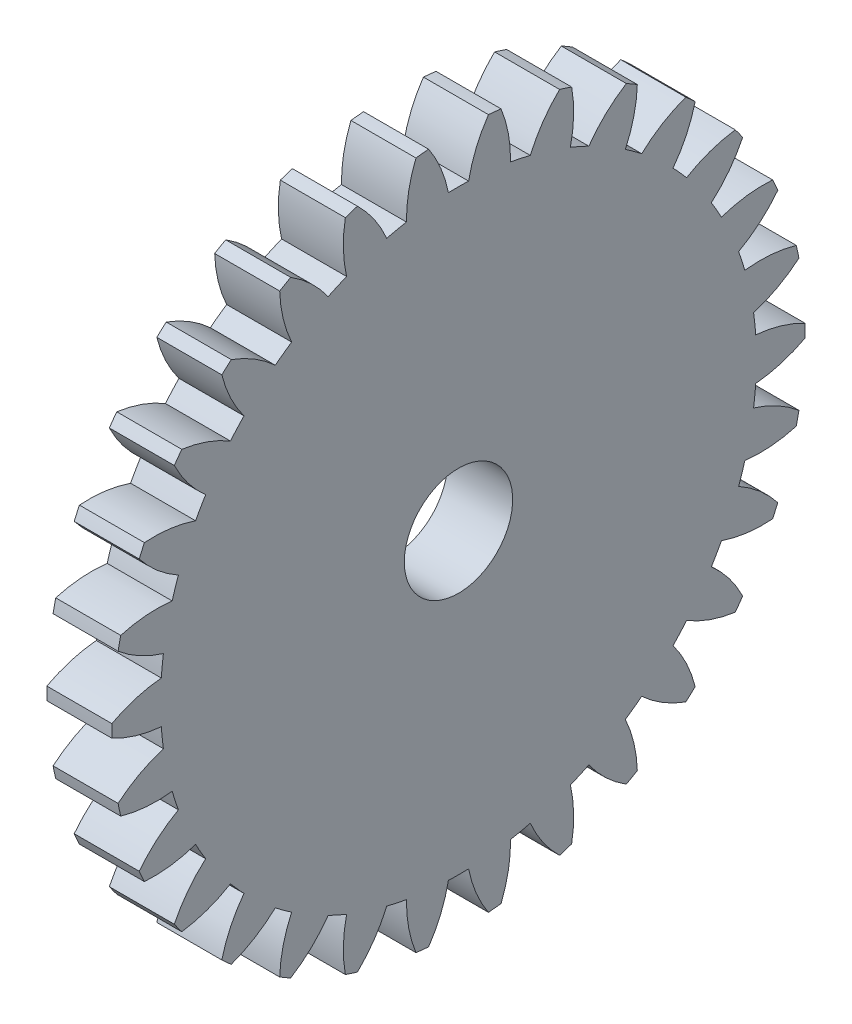
SolidWorks part; units mm, degrees
ref_plane "Plane1" through (0, 0, 0) normal (0, 0, 1) x (1, 0, 0)
ref_plane "Plane2" through (0, 0, 0) normal (0, 1, 0) x (1, 0, 0)
ref_plane "Plane3" through (0, 0, 0) normal (1, 0, 0) x (0, 0, -1)
sketch "HoldingSke" plane through (0, 0, 0) normal (0, 1, 0) x (1, 0, 0)
  line L0 (0, 0) -> (0.866, -0.5)
  line L1 (-15, 0) -> (100, 0) construction
  line L2 (0, 0) -> (-2.1039, 2.3779)
  line L3 (0, 0) -> (-11.863, 4.5341)
  line L4 (0, 0) -> (7.479, 4.318)
  line L5 (0, 0) -> (-46.8476, -17.4728)
  line L6 (0, 0) -> (-2.4869, -1.6779)
  line L7 (-2.1039, 2.3779) -> (8.6586, 51.2059)
  line L8 (-76.2, 54.61) -> (-75.3, 54.61)
  line L9 (-71.009, 38.7566) -> (-53.1078, 45.2721)
  line L10 (-76.2, 71.12) -> (104.1128, 71.12)
  line L11 (0, 0) -> (-3, 0)
  line L12 (-76.2, 101.6) -> (-76.162, 101.6)
  line L13 (24.9733, 27.94) -> (52.9518, 28.4284)
  line L14 (24.9733, 27.94) -> (24.9743, 27.94)
  line L15 (24.9733, 27.94) -> (100.4006, 29.5858)
  line L16 (-63.627, -1) -> (-12.827, -1)
  circle A0 centre (0, 0) radius 2.5
  circle A1 centre (0, 0) radius 13.749
  circle A2 centre (0, 0) radius 37.5
  circle A3 centre (0, 0) radius 2.5
  dimension "MHD" = 27.498
  dimension "Hub_dia" = 75
  dimension "Bore" = 5
  dimension "MBD" = 5
  dimension "Num_teeth" = 30
  dimension "Pitch_radius" = 180.3128
  dimension "Pitch" = 1
  dimension "Width" = 3
  dimension "Overall_len" = 50
  dimension "Show_teeth" = 30
  dimension "Thickness" = 3
  dimension "OAL" = 50.0001
  dimension "T_dim" = 0.9
  dimension "Ap" = 20
  dimension "H" = 19.05
  dimension "Backlash" = 0.038
  dimension "Addendum_fac" = 1
  dimension "Dedendum_fac" = 1.25
  dimension "Clearance_fac" = 0.25
  dimension "Dedendum_add" = 0.001
  dimension "Module" = 1
sketch "BasProSke" plane through (0, 0, 0) normal (0, 1, 0) x (1, 0, 0)
  line L0 (-10, 0) -> (60, 0) construction
  line L1 (0, 0) -> (0, 16)
  line L2 (0, 0) -> (3, 0)
  line L3 (3, 0) -> (3, 16)
  line L4 (3, 16) -> (0, 16)
  dimension "Diameter" = 32
  dimension "Thickness" = 3
revolve "Base-Revolve" add sketch "BasProSke" angle 360 about L0
sketch "TooCutSke" plane through (0, 0, 0) normal (1, 0, 0) x (0, 0, -1)
  line L1 (0, 0) -> (0, 107) construction
  line L2 (0, 0) -> (-0.8515, 14.9758) construction
  line L3 (0, 0) -> (-3.1323, 29.8014) construction
  line L4 (-0.8515, 14.9758) -> (-1.5661, 14.9007) construction
  arc A0 (0.4664, 13.7411) -> (-0.4664, 13.7411) centre (0, 0) ccw
  arc A1 (1.3975, 15.9644) -> (-1.3975, 15.9644) centre (0, 0) ccw
  circle A2 centre (0, 0) radius 15 construction
  circle A3 centre (0, 0) radius 14.0954 construction
  arc A4 (-0.4664, 13.7411) -> (-1.3975, 15.9644) centre (-6.3534, 12.5823) ccw
  arc A5 (1.3975, 15.9644) -> (0.4664, 13.7411) centre (6.3534, 12.5823) ccw
  dimension "Root_dia" = 27.498
  dimension "Overcut_dia" = 32.0508
  dimension "Pitch_dia" = 30
  dimension "Base_dia" = 28.1908
  dimension "Flank_rad" = 6
  dimension "Half_ang" = 6
  dimension "Half_CT" = 0.7185
extrude "ToothCut" cut sketch "TooCutSke" along normal through all
fillet "Breaks" [suppressed] radius 0.02
fillet "RootFillets" [suppressed] radius 0.251
pattern_circular "TeethCuts" count 30 every 12 about axis through (-10, 0, 0) along (1, 0, 0) of "ToothCut", "RootFillets", "Breaks"
sketch "HubNeaOneSke" plane through (0, 0, 0) normal (-1, 0, 0) x (0, 0, 1)
  circle A0 centre (0, 0) radius 13.749
  dimension "Diameter" = 27.498
extrude "HubNearOne" [suppressed] add sketch "HubNeaOneSke" along normal blind 47.0001
sketch "HubNeaBotSke" plane through (0, 0, 0) normal (-1, 0, 0) x (0, 0, 1)
  circle A0 centre (0, 0) radius 13.749
  dimension "Diameter" = 27.498
extrude "HubNearBoth" [suppressed] add sketch "HubNeaBotSke" along normal blind 23.5
ref_plane "FarPln" through (3, 0, 0) normal (1, 0, 0) x (0, 0, -1)
sketch "HubFarSke" plane through (3, 0, 0) normal (1, 0, 0) x (0, 0, -1)
  circle A0 centre (0, 0) radius 13.749
  dimension "Diameter" = 27.498
extrude "HubFar" [suppressed] add sketch "HubFarSke" along normal blind 23.5
sketch "BorSke" plane through (0, 0, 0) normal (1, 0, 0) x (0, 0, -1)
  circle A0 centre (0, 0) radius 2.5
  dimension "Diameter" = 5
extrude "Bore" cut sketch "BorSke" along normal mid plane 100.0001
sketch "KeySke" plane through (0, 0, 0) normal (1, 0, 0) x (0, 0, -1)
  line L0 (-1, 0) -> (-1, 3.4)
  line L1 (-1, 3.4) -> (1, 3.4)
  line L2 (1, 3.4) -> (1, 0)
  line L3 (0, 0) -> (0, 34) construction
  line L4 (-1, 0) -> (1, 0)
  dimension "Offset" = 3.4
  dimension "Width" = 2
extrude "Keyway" [suppressed] cut sketch "KeySke" along normal mid plane 100.0001
pattern_circular "Keyway2" [suppressed] count 2 every 90 about axis through (-10, 0, 0) along (1, 0, 0)
equation "' \"Module@HoldingSke\" = 6.35"
equation "' \"Num_teeth@HoldingSke\" = 12"
equation "' \"Ap@HoldingSke\" =  20"
equation "' \"Width@HoldingSke\" = 0.5 * 25.4"
equation "' \"Hub_dia@HoldingSke\"= 1 * 25.4"
equation "' \"Overall_len@HoldingSke\" = 1.0 * 25.4"
equation "' \"Bore@HoldingSke\" = 0.75 * 25.4"
equation "' \"T_dim@HoldingSke\" = 0.1 * 25.4"
equation "' \"Width@KeySke\" = 0.25 * 25.4"
equation "' \"Show_teeth@HoldingSke\" = 13"
equation "' \"Backlash@HoldingSke\" = 0.009 * 25.4"
equation "' \"Addendum_fac@HoldingSke\" = 1.0"
equation "' \"Dedendum_fac@HoldingSke\" = 1.25"
equation "' \"Dedendum_add@HoldingSke\" = 0.00005 * 25.4"
equation "' \"Clearance_fac@HoldingSke\" = 0.25"
equation "\"Pitch@HoldingSke\" = 1 / \"Module@HoldingSke\""
equation "\"Overcut_dia@TooCutSke\" = (\"Num_teeth@HoldingSke\" + 2 * \"Addendum_fac@HoldingSke\") / \"Pitch@HoldingSke\" + 0.002 * 25.4"
equation "\"Pitch_dia@TooCutSke\" = \"Num_teeth@HoldingSke\" / \"Pitch@HoldingSke\""
equation "\"Base_dia@TooCutSke\" = \"Num_teeth@HoldingSke\" / \"Pitch@HoldingSke\" * cos((\"Ap@HoldingSke\"  * 3.14159265 / 180))"
equation "\"Root_dia@TooCutSke\" = (\"Num_teeth@HoldingSke\" + 2) / \"Pitch@HoldingSke\" - 2 * (\"Addendum_fac@HoldingSke\" + \"Dedendum_fac@HoldingSke\") / \"Pitch@HoldingSke\" - \"Dedendum_add@HoldingSke\" * 2"
equation "\"Half_ang@TooCutSke\" = 180 / \"Num_teeth@HoldingSke\""
equation "\"Half_CT@TooCutSke\" = \"Num_teeth@HoldingSke\" / \"Pitch@HoldingSke\" * sin((3.14159265 / 2 / \"Num_teeth@HoldingSke\")) / 2 - 7 * \"Backlash@HoldingSke\" / 4"
equation "\"Flank_rad@TooCutSke\" = \"Num_teeth@HoldingSke\" / \"Pitch@HoldingSke\" / 5"
equation "\"Radius@RootFillets\" = \"Clearance_fac@HoldingSke\" / \"Pitch@HoldingSke\" + \"Dedendum_add@HoldingSke\""
equation "\"Break_rad@Breaks\" = 0.02 / \"Pitch@HoldingSke\""
equation "\"Thickness@HoldingSke\" = \"Width@HoldingSke\""
equation "\"OAL@HoldingSke\" = \"Thickness@HoldingSke\""
equation "\"MHD@HoldingSke\" = (\"Num_teeth@HoldingSke\" + 2) / \"Pitch@HoldingSke\" - 2 * (\"Addendum_fac@HoldingSke\" + \"Dedendum_fac@HoldingSke\")  / \"Pitch@HoldingSke\" - \"Dedendum_add@HoldingSke\" * 2"
equation "\"MBD@HoldingSke\" = (\"Num_teeth@HoldingSke\" + 2) / \"Pitch@HoldingSke\" - 2 * (\"Addendum_fac@HoldingSke\" + \"Dedendum_fac@HoldingSke\")  / \"Pitch@HoldingSke\" - \"Dedendum_add@HoldingSke\" * 2 - 0.002 * 25.4"
equation "\"MHD@HoldingSke\" = ((sgn( \"MHD@HoldingSke\" - \"Hub_dia@HoldingSke\" )-1)*( \"MHD@HoldingSke\" - \"Hub_dia@HoldingSke\" ))/-2+ \"Hub_dia@HoldingSke\""
equation "\"MBD@HoldingSke\" = ((sgn( \"MBD@HoldingSke\" - \"Bore@HoldingSke\" )-1)*( \"MBD@HoldingSke\" - \"Bore@HoldingSke\" ))/-2+ \"Bore@HoldingSke\""
equation "\"OAL@HoldingSke\" = ((sgn( \"OAL@HoldingSke\" - \"Overall_len@HoldingSke\" )+1)*( \"OAL@HoldingSke\" - \"Overall_len@HoldingSke\" ))/2 + \"Overall_len@HoldingSke\" + 0.000002 * 25.4"
equation "\"Num_teeth@TeethCuts\" = int( \"Show_teeth@HoldingSke\" ) + 1"
equation "\"Num_teeth@TeethCuts\" = ((sgn( \"Num_teeth@TeethCuts\" - \"Num_teeth@HoldingSke\" )-1)*( \"Num_teeth@TeethCuts\" - \"Num_teeth@HoldingSke\" ))/-2+ \"Num_teeth@HoldingSke\""
equation "\"Num_teeth@TeethCuts\" = ((sgn( \"Num_teeth@TeethCuts\" - 2.0)+1)*( \"Num_teeth@TeethCuts\" - 2.0))/2 +2.0"
equation "\"Angle@TeethCuts\" = 360.0 / \"Num_teeth@HoldingSke\""
equation "\"Diameter@BasProSke\" = (\"Num_teeth@HoldingSke\" + 2 * \"Addendum_fac@HoldingSke\") / \"Pitch@HoldingSke\""
equation "\"Thickness@BasProSke\"  = \"Thickness@HoldingSke\""
equation "' \"Fillet_rad@BasProSke\" =  \"Thickness@HoldingSke\" * 0.05"
equation "\"MHD@HoldingSke\" = ((sgn( \"MHD@HoldingSke\" - \"Root_dia@TooCutSke\" )-1)*( \"MHD@HoldingSke\" - \"Root_dia@TooCutSke\" ))/-2+ \"Root_dia@TooCutSke\""
equation "\"Diameter@HubNeaOneSke\" = \"MHD@HoldingSke\""
equation "\"Length@HubNearOne\" = \"OAL@HoldingSke\" - \"Thickness@BasProSke\""
equation "\"Diameter@HubNeaBotSke\" = \"MHD@HoldingSke\""
equation "\"Length@HubNearBoth\" = ( \"OAL@HoldingSke\" - \"Thickness@BasProSke\" ) / 2.0"
equation "\"Thickness@FarPln\" = \"Thickness@BasProSke\""
equation "\"Diameter@HubFarSke\" = \"MHD@HoldingSke\""
equation "\"Length@HubFar\" = ( \"OAL@HoldingSke\" - \"Thickness@BasProSke\" ) / 2.0"
equation "\"Diameter@BorSke\" = \"MBD@HoldingSke\""
equation "\"D1@Bore\" = \"OAL@HoldingSke\" * 2.0"
equation "\"D1@Keyway\" = \"OAL@HoldingSke\" * 2.0"
equation "\"Offset@KeySke\" = \"T_dim@HoldingSke\" + \"MBD@HoldingSke\" / 2.0"
